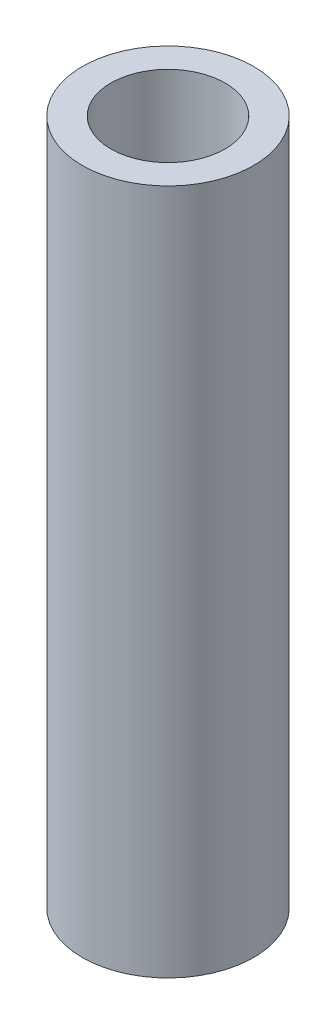
SolidWorks part; units mm, degrees
ref_plane "Front Plane" through (0, 0, 0) normal (0, 0, 1) x (1, 0, 0)
ref_plane "Top Plane" through (0, 0, 0) normal (0, 1, 0) x (1, 0, 0)
ref_plane "Right Plane" through (0, 0, 0) normal (1, 0, 0) x (0, 0, -1)
sketch "Sketch1" plane through (0, 0, 0) normal (0, 1, 0) x (1, 0, 0)
  circle A0 centre (0, 0) radius 7.5
  dimension "D1" = 15
extrude "Boss-Extrude1" add sketch "Sketch1" along normal blind 60
sketch "Sketch2" plane through (0, 60, 0) normal (0, 1, 0) x (1, 0, 0)
  circle A0 centre (0, 0) radius 5
  dimension "D1" = 10
extrude "Cut-Extrude1" cut sketch "Sketch2" against normal blind 15
ref_plane "Plane1" through (0, 0, -7.5) normal (0, 0, -1) x (-1, 0, 0)
sketch "Sketch3" plane through (0, 0, -7.5) normal (0, 0, -1) x (-1, 0, 0)
  line L1 (2.625, 19.875) -> (-2.625, 19.875)
  line L2 (2.625, 19.875) -> (2.625, 40.125)
  line L3 (2.625, 40.125) -> (-2.625, 40.125)
  line L4 (-2.625, 19.875) -> (-2.625, 40.125)
  line L5 (2.625, 19.875) -> (-2.625, 40.125) construction
  line L6 (2.625, 40.125) -> (-2.625, 19.875) construction
  point P0 (0, 30)
  dimension "D1" = 5.25
  dimension "D2" = 20.25
  dimension "D3" = 30
extrude "Cut-Extrude2" cut sketch "Sketch3" against normal blind 7.5
